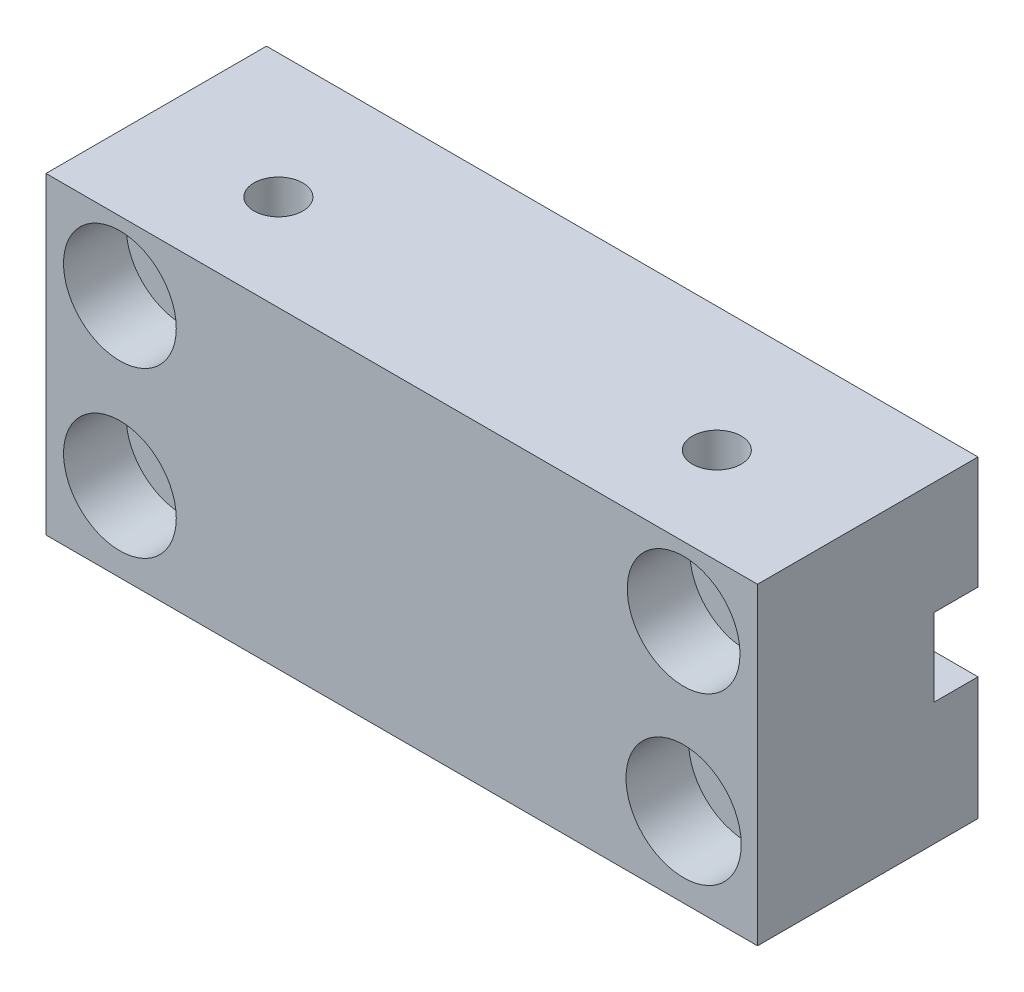
SolidWorks part; units mm, degrees
ref_plane "Front Plane" through (0, 0, 0) normal (0, 0, 1) x (1, 0, 0)
ref_plane "Top Plane" through (0, 0, 0) normal (0, 1, 0) x (1, 0, 0)
ref_plane "Right Plane" through (0, 0, 0) normal (1, 0, 0) x (0, 0, -1)
sketch "Sketch1" plane through (0, 0, 0) normal (0, 0, 1) x (1, 0, 0)
  line L0 (-28.575, 8.8755) -> (28.575, 8.8755) construction
  line L1 (-36.068, 15.875) -> (36.068, 15.875)
  line L2 (-36.068, 15.875) -> (-36.068, -15.875)
  line L3 (-36.068, -15.875) -> (36.068, -15.875)
  line L4 (36.068, 15.875) -> (36.068, -15.875)
  line L5 (-36.068, 15.875) -> (36.068, -15.875) construction
  line L6 (-36.068, -15.875) -> (36.068, 15.875) construction
  circle A0 centre (-28.575, 8.8755) radius 5.715
  circle A1 centre (28.575, 8.8755) radius 5.715
  circle A2 centre (-28.575, -7.8003) radius 5.715
  circle A3 centre (28.575, -7.8003) radius 5.842
  point P0 (0, 0)
  point P15 (0, 8.8755)
  dimension "D4" = 11.43
  dimension "D5" = 11.43
  dimension "D1" = 72.136
  dimension "D2" = 31.75
  dimension "D3" = 57.15
extrude "Boss-Extrude1" add sketch "Sketch1" along normal blind 22.352
sketch "Sketch4" plane through (0, 0, 0) normal (0, 0, 1) x (1, 0, 0)
  circle A0 centre (-28.575, 8.8755) radius 5.715
  circle A1 centre (-28.575, 8.8755) radius 2.54
  circle A2 centre (-28.575, -7.8003) radius 5.715
  circle A3 centre (-28.575, -7.8003) radius 2.54
  circle A4 centre (28.575, 8.8755) radius 5.715
  circle A5 centre (28.575, 8.8755) radius 2.54
  circle A6 centre (28.575, -7.8003) radius 5.842
  circle A7 centre (28.575, -7.8003) radius 2.54
extrude "Boss-Extrude2" add sketch "Sketch4" along normal offset from surface (16.002 mm away) 6.35 up to face at (34.417, -7.8003, 22.352)
cosmetic thread "Cosmetic Thread3" parameters "D2"=6.35
cosmetic thread "Cosmetic Thread4" parameters "D2"=6.35
cosmetic thread "Cosmetic Thread5" parameters "D2"=6.35
cosmetic thread "Cosmetic Thread6" parameters "D2"=6.35
sketch "Sketch2" plane through (0, -15.875, 0) normal (0, -1, 0) x (1, 0, 0)
  line L0 (-22.225, 12.6365) -> (22.225, 12.6365) construction
  line L1 (-36.068, 0) -> (36.068, 0) construction
  circle A0 centre (-22.225, 12.6365) radius 2.4765
  circle A1 centre (22.225, 12.6365) radius 2.4765
  point P3 (0, 12.6365)
  point P5 (-22.225, 10.16)
  dimension "D3" = 4.953
  dimension "D1" = 44.45
  dimension "D2" = 10.16
extrude "Cut-Extrude1" cut sketch "Sketch2" against normal through all
cosmetic thread "Cosmetic Thread1" parameters "D2"=6.35
cosmetic thread "Cosmetic Thread2" parameters "D2"=6.35
sketch "Sketch5" plane through (-36.068, 0, 0) normal (-1, 0, 0) x (0, 0, 1)
  line L0 (0, 15.875) -> (0, -15.875) construction
  line L1 (0, 4.445) -> (4.445, 4.445)
  line L2 (0, 4.445) -> (0, -3.429)
  line L3 (0, -3.429) -> (4.445, -3.429)
  line L4 (4.445, 4.445) -> (4.445, -3.429)
  line L5 (22.352, 15.875) -> (0, 15.875) construction
  dimension "D1" = 4.445
  dimension "D2" = 11.43
  dimension "D3" = 7.874
extrude "Cut-Extrude2" cut sketch "Sketch5" against normal through all
